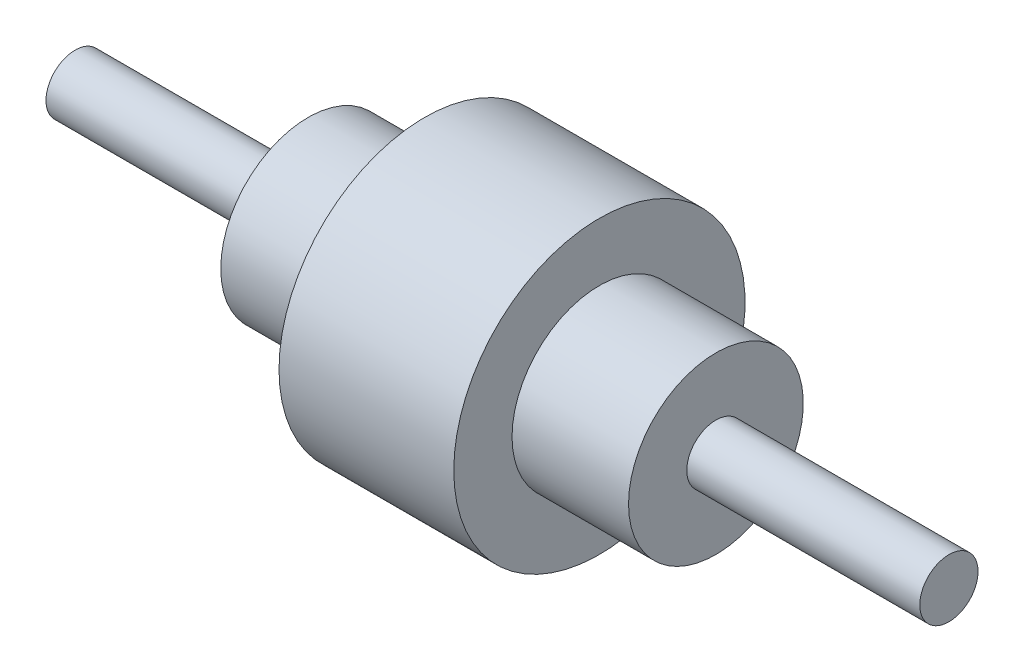
SolidWorks part; units mm, degrees
ref_plane "Front Plane" through (0, 0, 0) normal (0, 0, 1) x (1, 0, 0)
ref_plane "Top Plane" through (0, 0, 0) normal (0, 1, 0) x (1, 0, 0)
ref_plane "Right Plane" through (0, 0, 0) normal (1, 0, 0) x (0, 0, -1)
sketch "Sketch1" plane through (0, 0, 0) normal (0, 0, 1) x (1, 0, 0)
  line L0 (0, 0) -> (392.3331, 0) construction
  line L2 (0, 0) -> (80, 0)
  line L3 (0, 0) -> (0, 10)
  line L4 (0, 10) -> (80, 10)
  line L5 (80, 0) -> (80, 10)
  line L6 (80, 0) -> (120, 0)
  line L7 (80, 0) -> (80, 30)
  line L8 (80, 30) -> (120, 30)
  line L9 (120, 0) -> (120, 30)
  line L10 (120, 0) -> (180, 0)
  line L11 (120, 0) -> (120, 50)
  line L12 (120, 50) -> (180, 50)
  line L13 (180, 0) -> (180, 50)
  line L14 (180, 30) -> (220, 30)
  line L15 (180, 30) -> (180, 0)
  line L16 (180, 0) -> (220, 0)
  line L17 (220, 30) -> (220, 0)
  line L18 (220, 10) -> (300, 10)
  line L19 (220, 10) -> (220, 0)
  line L20 (220, 0) -> (300, 0)
  line L21 (300, 10) -> (300, 0)
  dimension "D1" = 10
  dimension "D2" = 30
  dimension "D3" = 50
  dimension "D4" = 80
  dimension "D5" = 40
  dimension "D6" = 60
revolve "Revolve1" add sketch "Sketch1" angle 360 about L0
